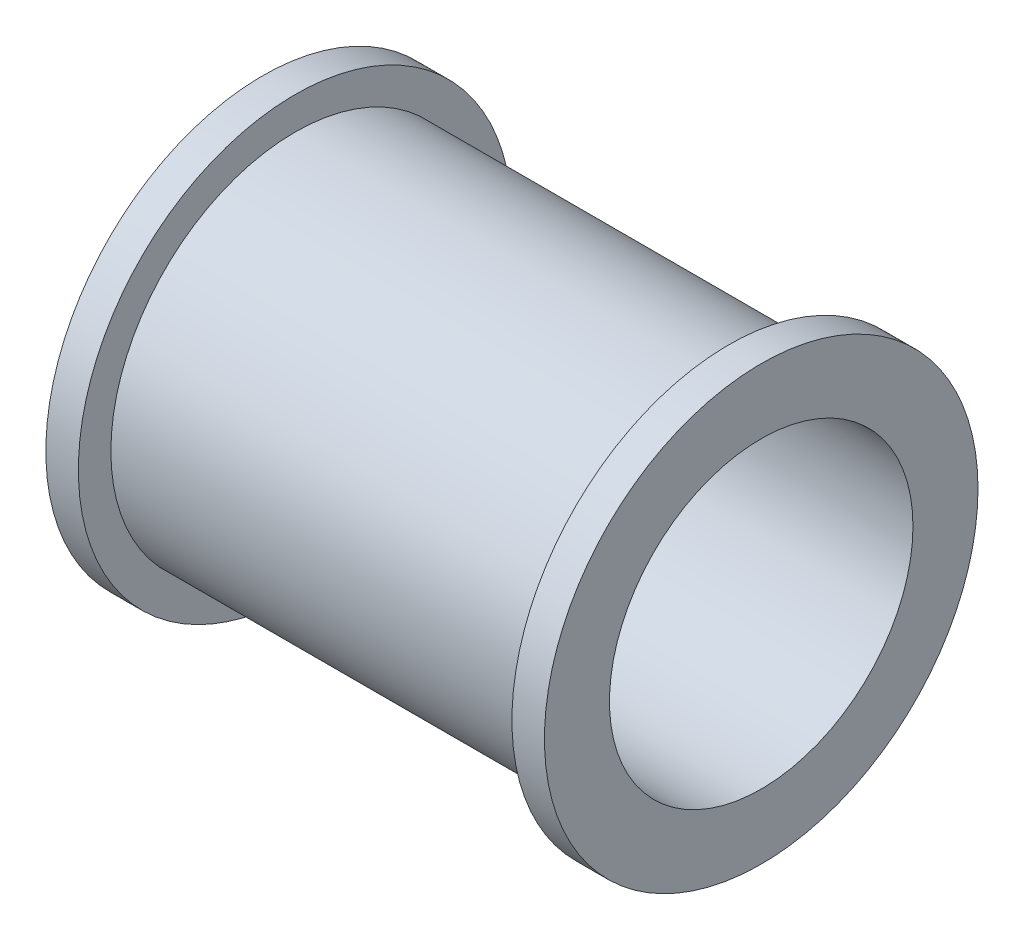
SolidWorks part; units mm, degrees
material "Резина"
ref_plane "Спереди" through (0, 0, 0) normal (0, 0, 1) x (1, 0, 0)
ref_plane "Сверху" through (0, 0, 0) normal (0, 1, 0) x (1, 0, 0)
ref_plane "Справа" through (0, 0, 0) normal (1, 0, 0) x (0, 0, -1)
sketch "Эскиз2" plane through (0, 0, 0) normal (0, 1, 0) x (1, 0, 0)
  line L0 (0, 0) -> (0, 10)
  line L1 (0, 10) -> (1.5, 10)
  line L2 (1.5, 10) -> (1.5, 8.5)
  line L3 (1.5, 8.5) -> (21.5, 8.5)
  line L4 (23, 0) -> (0, 0)
  line L5 (11.5, 8.5) -> (11.5, 0) construction
  line L6 (23, 0) -> (23, 10)
  line L7 (23, 10) -> (21.5, 10)
  line L8 (21.5, 10) -> (21.5, 8.5)
  dimension "D1" = 1.5
  dimension "D2" = 8.5
  dimension "D3" = 10
  dimension "D4" = 10
revolve "Повернуть1" add sketch "Эскиз2" angle 360 about L4
sketch "Эскиз3" plane through (23, 0, 0) normal (1, 0, 0) x (0, 0, -1)
  circle A0 centre (0, 0) radius 7
  dimension "D1" = 14
extrude "Вырез-Вытянуть1" cut sketch "Эскиз3" against normal through all
equation "\"D3@Эскиз2\"=\"D2@Эскиз2\"+1.5"
